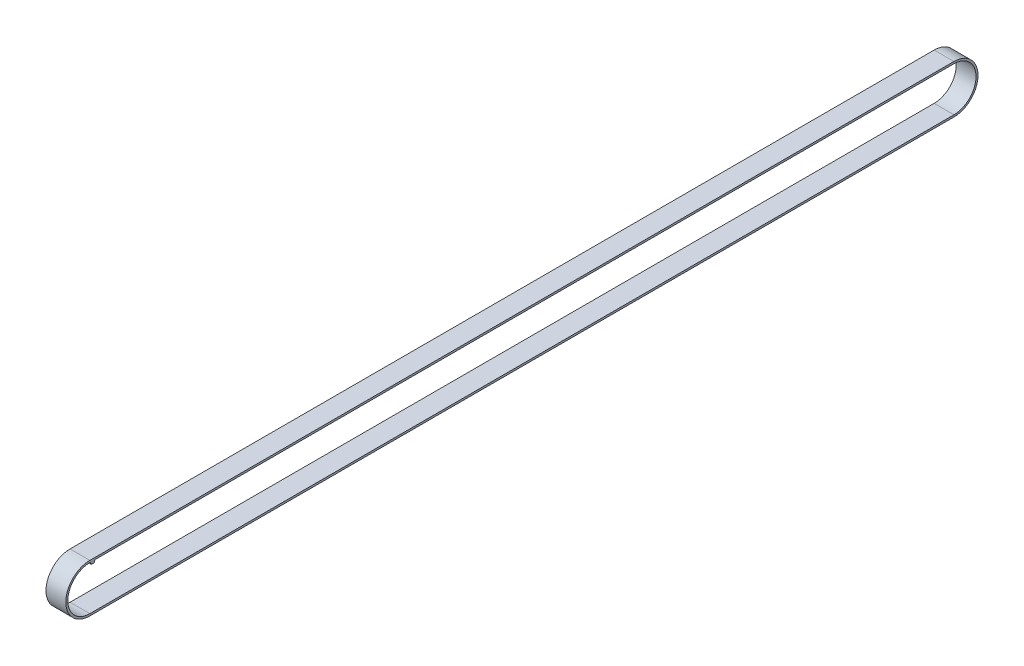
SolidWorks part; units mm, degrees
ref_plane "Front" through (0, 0, 0) normal (0, 0, 1) x (1, 0, 0)
ref_plane "Top" through (0, 0, 0) normal (0, 1, 0) x (1, 0, 0)
ref_plane "Right" through (0, 0, 0) normal (1, 0, 0) x (0, 0, -1)
sketch "Sketch1" plane through (0, 0, 0) normal (1, 0, 0) x (0, 0, -1)
  line L0 (0, 0) -> (262, 0) construction
  line L1 (0, 7.3) -> (262, 7.3)
  line L2 (0, -7.3) -> (262, -7.3)
  line L3 (0, 0) -> (262, 0) construction
  line L4 (0, 6.7) -> (262, 6.7)
  line L5 (0, -6.7) -> (262, -6.7)
  arc A0 (0, 7.3) -> (0, -7.3) centre (0, 0) ccw
  arc A1 (262, -7.3) -> (262, 7.3) centre (262, 0) ccw
  arc A2 (0, 6.7) -> (0, -6.7) centre (0, 0) ccw
  arc A3 (262, -6.7) -> (262, 6.7) centre (262, 0) ccw
  point P3 (131, 0)
  point P10 (131, 0)
  dimension "D2" = 7.3
  dimension "D1" = 262
  dimension "D3" = 0.6
extrude "Boss-Extrude1" add sketch "Sketch1" along normal blind 6
curve "CompCurve1"
sketch "Sketch2" plane through (0, 0, 0) normal (1, 0, 0) x (0, 0, -1)
  line L0 (0.1879, 6.5684) -> (0.3469, 6.1316)
  line L1 (0.5349, 6) -> (1.159, 6)
  line L2 (1.3469, 6.1316) -> (1.5059, 6.5684)
  line L3 (262, 6.7) -> (0, 6.7) construction
  line L4 (0.8469, 15.4872) -> (0.8469, 12.6294) construction
  line L5 (0, 6.7) -> (1.6938, 6.7)
  arc A0 (0.3469, 6.1316) -> (0.5349, 6) centre (0.5349, 6.2) ccw
  arc A1 (1.159, 6) -> (1.3469, 6.1316) centre (1.159, 6.2) ccw
  arc A2 (1.5059, 6.5684) -> (1.6938, 6.7) centre (1.6938, 6.5) cw
  arc A3 (0.1879, 6.5684) -> (0, 6.7) centre (0, 6.5) ccw
  point P16 (0.3948, 6)
  point P19 (1.299, 6)
  point P22 (1.6938, 6.7)
  point P25 (0, 6.7)
  dimension "D3" = 0.2
  dimension "D1" = 40
  dimension "D2" = 0.7
  dimension "D4" = 1
extrude "Boss-Extrude2" add sketch "Sketch2" along normal through all
